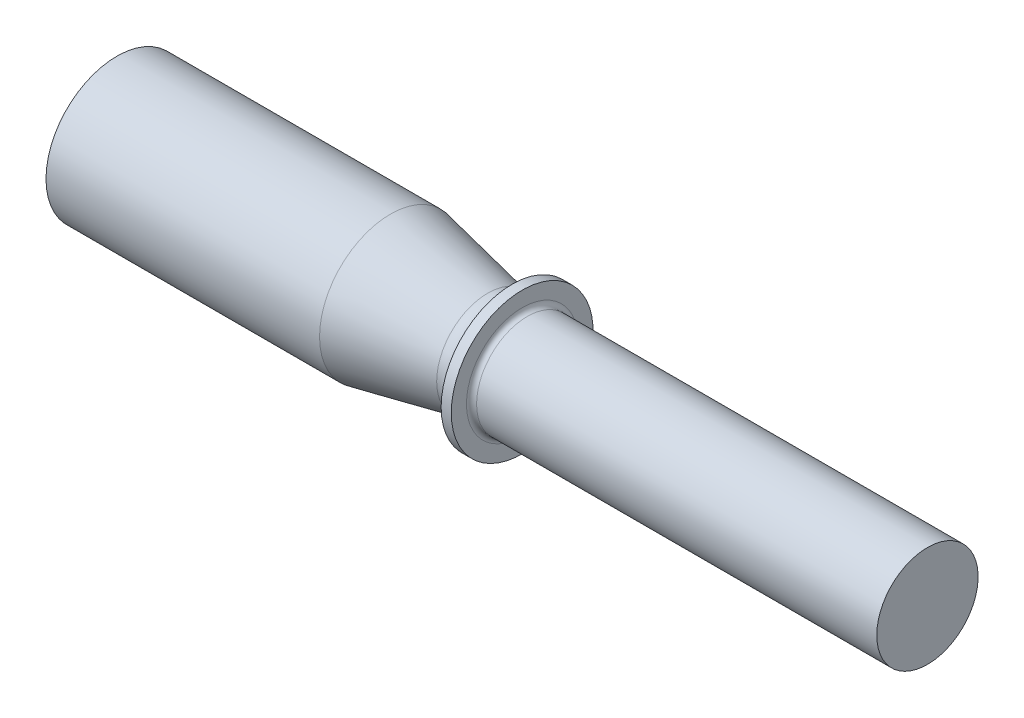
SolidWorks part; units mm, degrees
ref_plane "Front" through (0, 0, 0) normal (0, 0, 1) x (1, 0, 0)
ref_plane "Top" through (0, 0, 0) normal (0, 1, 0) x (1, 0, 0)
ref_plane "Right" through (0, 0, 0) normal (1, 0, 0) x (0, 0, -1)
sketch "Sketch1" plane through (0, 0, 0) normal (0, 0, 1) x (1, 0, 0)
  line L0 (-70.8914, 0) -> (68.8107, 0) construction
  line L1 (0, 17.78) -> (0, 0)
  line L2 (0, 0) -> (203.2, 0)
  line L3 (203.2, 0) -> (203.2, 12.7)
  line L4 (203.2, 12.7) -> (101.6, 12.7)
  line L5 (101.6, 12.7) -> (101.6, 17.78)
  line L6 (101.6, 17.78) -> (99.06, 17.78)
  line L7 (0, 17.78) -> (68.58, 17.78)
  line L8 (68.58, 17.78) -> (92.964, 12.8026)
  arc A0 (92.964, 12.8026) -> (99.06, 17.78) centre (93.98, 17.78) ccw
  dimension "D5" = 5.08
  dimension "D1" = 203.2
  dimension "D2" = 101.6
  dimension "D3" = 12.7
  dimension "D4" = 17.78
  dimension "D6" = 5.08
  dimension "D7" = 2.54
  dimension "D8" = 68.58
revolve "Revolve1" add sketch "Sketch1" angle 360 about L0
fillet "Fillet1" radius 1.27 1 edges at (101.6, 0, 12.7)
